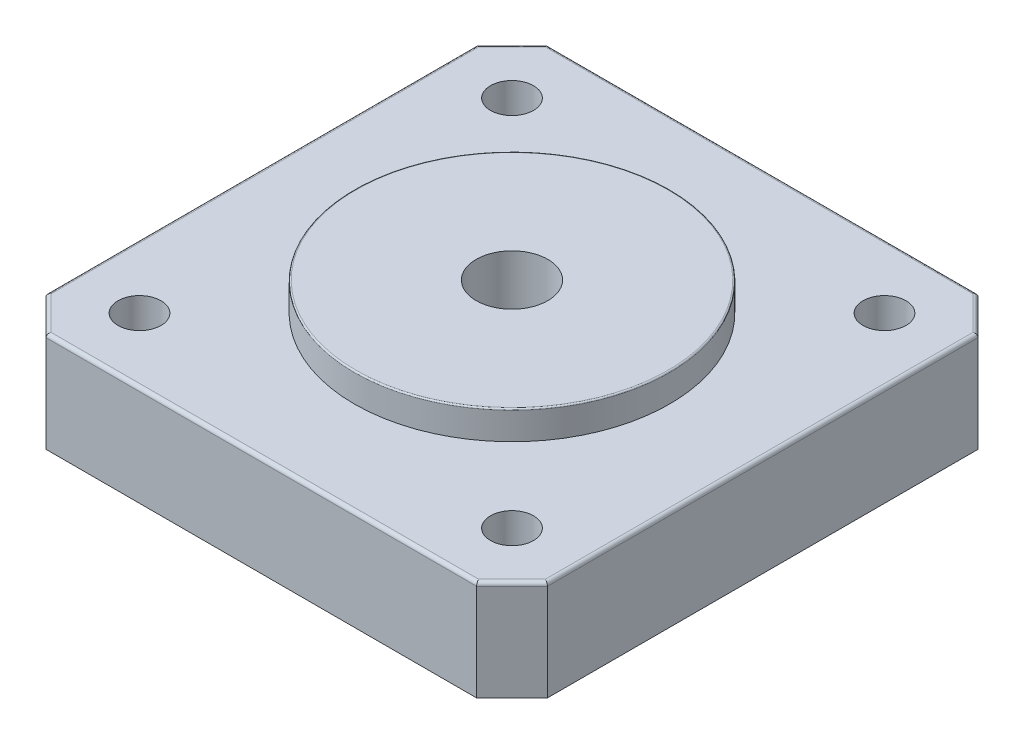
SolidWorks part; units mm, degrees
material "Aleación 1060"
ref_plane "Alzado" through (0, 0, 0) normal (0, 0, 1) x (1, 0, 0)
ref_plane "Planta" through (0, 0, 0) normal (0, 1, 0) x (1, 0, 0)
ref_plane "Vista lateral" through (0, 0, 0) normal (1, 0, 0) x (0, 0, -1)
sketch "Croquis1" plane through (0, 0, 0) normal (0, 1, 0) x (1, 0, 0)
  line L0 (0, 32.5269) -> (2.4731, 35)
  line L1 (2.4731, 0) -> (32.5269, 0)
  line L2 (0, 2.4731) -> (0, 32.5269)
  line L3 (2.4731, 35) -> (32.5269, 35)
  line L4 (35, 2.4731) -> (35, 32.5269)
  line L5 (0, 0) -> (35, 35) construction
  line L6 (0, 35) -> (35, 0) construction
  line L7 (32.5269, 35) -> (35, 32.5269)
  line L8 (35, 2.4731) -> (32.5269, 0)
  line L9 (2.4731, 0) -> (0, 2.4731)
  point P7 (17.5, 17.5)
  point P17 (17.5, 17.5)
  dimension "D1" = 35
  dimension "D2" = 35
  dimension "D3" = 4
  dimension "D4" = 23
extrude "Saliente-Extruir1" add sketch "Croquis1" along normal blind 7
sketch "Croquis2" plane through (0, 7, 0) normal (0, 1, 0) x (1, 0, 0)
  line L0 (0, 17.5) -> (35, 17.5) construction
  line L1 (0, 32.5269) -> (0, 2.4731) construction
  line L2 (35, 2.4731) -> (35, 32.5269) construction
  line L4 (32.5269, 35) -> (2.4731, 35) construction
  line L5 (17.5, 35) -> (17.5, 0) construction
  line L6 (2.4731, 0) -> (32.5269, 0) construction
  circle A0 centre (17.5, 17.5) radius 2.5
  dimension "D1" = 5
extrude "Cortar-Extruir1" cut sketch "Croquis2" against normal through all
sketch "Croquis3" plane through (0, 7, 0) normal (0, 1, 0) x (1, 0, 0)
  line L0 (4.5, 30.5) -> (30.5, 4.5) construction
  line L1 (4.5, 30.5) -> (30.5, 30.5) construction
  line L2 (4.5, 30.5) -> (4.5, 4.5) construction
  line L3 (4.5, 4.5) -> (30.5, 4.5) construction
  line L4 (30.5, 30.5) -> (30.5, 4.5) construction
  line L5 (4.5, 4.5) -> (30.5, 30.5) construction
  circle A0 centre (4.5, 30.5) radius 1.5
  circle A1 centre (30.5, 30.5) radius 1.5
  circle A2 centre (30.5, 4.5) radius 1.5
  circle A3 centre (4.5, 4.5) radius 1.5
  point P4 (17.5, 17.5)
  point P5 (17.5, 17.5)
  point P17 (17.5, 17.5)
  dimension "D3" = 3
  dimension "D1" = 26
  dimension "D2" = 26
  dimension "D4" = 4
extrude "Cortar-Extruir2" cut sketch "Croquis3" against normal through all
sketch "Croquis4" plane through (0, 7, 0) normal (0, 1, 0) x (1, 0, 0)
  circle A0 centre (17.5, 17.5) radius 11
  circle A1 centre (17.5, 17.5) radius 2.5
  dimension "D1" = 22
extrude "Saliente-Extruir2" add sketch "Croquis4" along normal blind 2
fillet "Redondeo1" radius 0.1 1 edges at (17.5, 9, -6.5)
fillet "Redondeo3" radius 0.25 8 edges at (1.2365, 7, -33.7635) (17.5, 7, -35) (33.7635, 7, -33.7635) (35, 7, -17.5) (33.7635, 7, -1.2365) (17.5, 7, 0) (1.2365, 7, -1.2365) (0, 7, -17.5)
